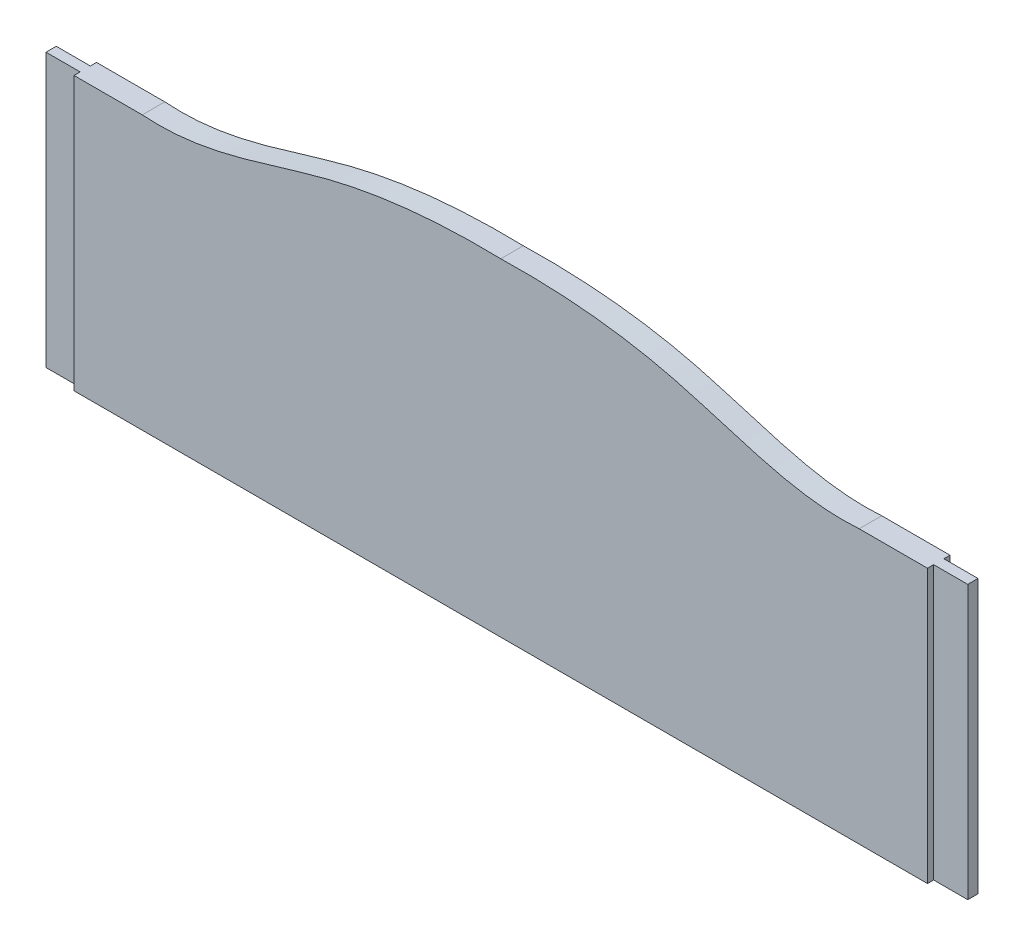
SolidWorks part; units mm, degrees
material "Cedar"
ref_plane "Front Plane" through (0, 0, 0) normal (0, 0, 1) x (1, 0, 0)
ref_plane "Top Plane" through (0, 0, 0) normal (0, 1, 0) x (1, 0, 0)
ref_plane "Right Plane" through (0, 0, 0) normal (1, 0, 0) x (0, 0, -1)
sketch "Sketch1" plane through (0, 0, 0) normal (0, 0, 1) x (1, 0, 0)
  line L8 (0, 0) -> (0, -480)
  line L10 (-525, -80) -> (-625, -80)
  line L12 (0, -480) -> (-625, -480)
  line L13 (-625, -80) -> (-625, -480)
  spline S0 degree 3 poles (0, 0) (-83.7015, 2.1027) (-263.2983, -12.317) (-428.0447, -87.2154) (-525, -80) knots 0 0 0 0 0.472196 1 1 1 1
  dimension "D1" = 80
  dimension "D2" = 400
  dimension "D3" = 150
  dimension "D4" = 78
  dimension "D5" = 100
  dimension "D6" = 55
  dimension "D7" = 100
  dimension "D8" = 15
  dimension "D9" = 140.2946
  dimension "D10" = 625
extrude "Boss-Extrude1" add sketch "Sketch1" along normal blind 33
sketch "Sketch2" plane through (0, -80, 0) normal (0, 1, 0) x (1, 0, 0)
  line L0 (-625, -33) -> (-625, 0) construction
  line L1 (-625, -9) -> (-675, -9)
  line L2 (-625, -9) -> (-625, -24)
  line L3 (-625, -24) -> (-675, -24)
  line L4 (-675, -9) -> (-675, -24)
  line L5 (-525, -33) -> (-625, -33) construction
  line L6 (-525, 0) -> (-625, 0) construction
  dimension "D1" = 15
  dimension "D2" = 9
  dimension "D3" = 9
  dimension "D4" = 50
extrude "Boss-Extrude2" add sketch "Sketch2" against normal through all
mirror "Mirror2" about plane through (0, 0, 0) normal (1, 0, 0) of "Boss-Extrude1", "Boss-Extrude2"
